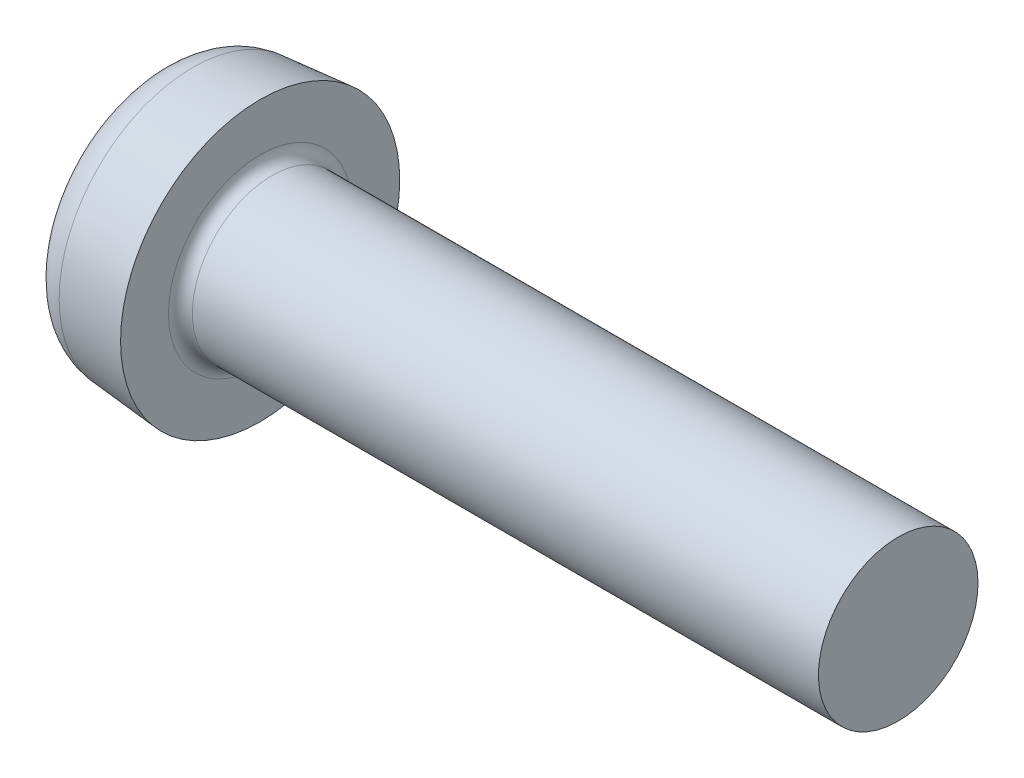
SolidWorks part; units mm, degrees
ref_plane "Front" through (0, 0, 0) normal (0, 0, 1) x (1, 0, 0)
ref_plane "Top" through (0, 0, 0) normal (0, 1, 0) x (1, 0, 0)
ref_plane "Right" through (0, 0, 0) normal (1, 0, 0) x (0, 0, -1)
sketch "Sketch1" plane through (0, 0, 0) normal (0, 0, 1) x (1, 0, 0)
  line L0 (18.6, 2) -> (4, 2)
  line L1 (2.6, 2.3) -> (2.6, 3.5)
  line L2 (2.6, 3.5) -> (0, 3.2725)
  line L3 (4, 2) -> (2.9, 2)
  line L4 (18.6, 2) -> (18.6, 0)
  line L5 (4.5158, 0) -> (-13.5157, 0) construction
  line L6 (18.6, 0) -> (0, 0)
  line L7 (0, 0) -> (0, 3.2725)
  arc A1 (2.6, 2.3) -> (2.9, 2) centre (2.9, 2.3) ccw
  dimension "d" = 4
  dimension "r" = 0.3
  dimension "l" = 16
  dimension "a" = 1.4
  dimension "D2" = 95
  dimension "k" = 2.6
  dimension "dk" = 7
revolve "Base" add sketch "Sketch1" angle 360 about L5
cosmetic thread "ThreadCosmetic1" [suppressed] parameters "bb"=16
sketch "Sketch6" plane through (0, 0, 0) normal (1, 0, 0) x (0, 0, -1)
  line L0 (-1.9271, 0) -> (2.0512, 0) construction
  line L1 (0, 1.8651) -> (0, -2.0207) construction
  line L2 (0.41, 0.41) -> (0.41, 2.05)
  line L3 (0.41, 2.05) -> (-0.41, 2.05)
  line L4 (-0.41, 0.41) -> (-0.41, 2.05)
  line L5 (0.41, 0.41) -> (2.05, 0.41)
  line L6 (2.05, 0.41) -> (2.05, -0.41)
  line L7 (-2.05, 0.41) -> (-2.05, -0.41)
  line L8 (-0.41, 0.41) -> (-2.05, 0.41)
  line L9 (-0.41, -0.41) -> (-2.05, -0.41)
  line L10 (0.41, -0.41) -> (2.05, -0.41)
  line L11 (-0.41, -0.41) -> (-0.41, -2.05)
  line L12 (0.41, -2.05) -> (-0.41, -2.05)
  line L13 (0.41, -0.41) -> (0.41, -2.05)
  point P16 (-2.05, 0)
  point P17 (2.05, 0)
extrude "CrossRecess" cut sketch "Sketch6" along normal blind 2.6
fillet "Fillet5" radius 0.3 4 edges at (1.3, -0.41, 0.41) (1.3, -0.41, -0.41) (1.3, 0.41, 0.41) (1.3, 0.41, -0.41)
sketch "Sketch8" [suppressed] plane through (0, 0, 0) normal (0, 0, 1) x (1, 0, 0)
  line L0 (12, 4) -> (8.2, 3.5)
  line L1 (8.2, 3.5) -> (5, 3.5)
  line L3 (50, -4) -> (50, 4) construction
  line L4 (5, -6.5) -> (5, 6.5) construction
  line L6 (5, 3.5) -> (5, 14)
  line L7 (5, 14) -> (12, 14)
  line L8 (12, 14) -> (12, 4)
  line L9 (52.4753, 0) -> (42.9594, 0) construction
  dimension "x" = 1.75
  dimension "THD_MINOR" = 3.242
  dimension "d" = 4
  dimension "D1" = 24
  dimension "b" = 38
fillet "HeadFillet" radius 1 1 edges at (0, 0, -3.2725)
draft "Draft1" type of draft neutral plane draft angle 20 faces to draft 4 face at (1.3, 0, 2.05) face at (1.3, -2.05, 0) face at (1.3, 0, -2.05) face at (1.3, 2.05, 0) neutral plane through (0, 0, 0) neutral plane normal (-1, 0, 0) parameters "D1"=20
sketch "Sketch7" plane through (0, 0, 0) normal (1, 0, 0) x (0, 0, -1)
  line L0 (-8.3217, 0) -> (7.4212, 0) construction
  line L1 (0, 7.4989) -> (0, -7.9646) construction
  line L2 (0, 0) -> (6.8599, 6.8599) construction
  line L3 (1.4496, 1.4496) -> (0, 0.7736)
  line L4 (0, 0) -> (-6.8599, 6.8599) construction
  line L5 (1.4496, 1.4496) -> (0.7736, 0)
  line L6 (1.4496, -1.4496) -> (0, -0.7736)
  line L7 (1.4496, -1.4496) -> (0.7736, 0)
  line L8 (-1.4496, -1.4496) -> (0, -0.7736)
  line L9 (-1.4496, -1.4496) -> (-0.7736, 0)
  line L10 (-1.4496, 1.4496) -> (0, 0.7736)
  line L11 (-1.4496, 1.4496) -> (-0.7736, 0)
  dimension "D2" = 20
  dimension "m" = 4.1
extrude "Cut-Extrude3" [suppressed] cut sketch "Sketch7" along normal blind 10 draft 20
sketch "Sketch10" plane through (0, 0, 0) normal (0, 0, 1) x (1, 0, 0)
  line L0 (18.6, 1.6718) -> (18.7895, 2)
  line L1 (18.7895, 2) -> (18.7895, 2.379)
  line L2 (18.7895, 2.379) -> (18.4105, 2.379)
  line L3 (18.4105, 2.379) -> (18.4105, 2)
  line L4 (18.4105, 2) -> (18.6, 1.6718)
  line L5 (18.6, 2) -> (4, 2) construction
  line L6 (18.6, 2) -> (18.6, 0) construction
  line L7 (0, 0) -> (57.111, 0) construction
  dimension "D1" = 0.379
revolve "Cut-Revolve10" [suppressed] cut sketch "Sketch10" angle 360 about L7
pattern_linear "LPattern10" [suppressed] count 35 spacing 0.4548 along (1, 0, 0)
equation "\"D1@Sketch6\" = \"m@Sketch6\" / 5"
equation "\"D1@Sketch8\" = \"d@Sketch8\" + 20"
equation "\"D1@Sketch10\" =  ( \"d@Sketch1\" - \"THD_MINOR@ThreadCosmetic1\" )  / 2"
equation "\"D3@LPattern10\" = \"D1@Sketch10\" * 1.2"
equation "\"D1@LPattern10\" = \"bb@ThreadCosmetic1\" / \"D3@LPattern10\" "
